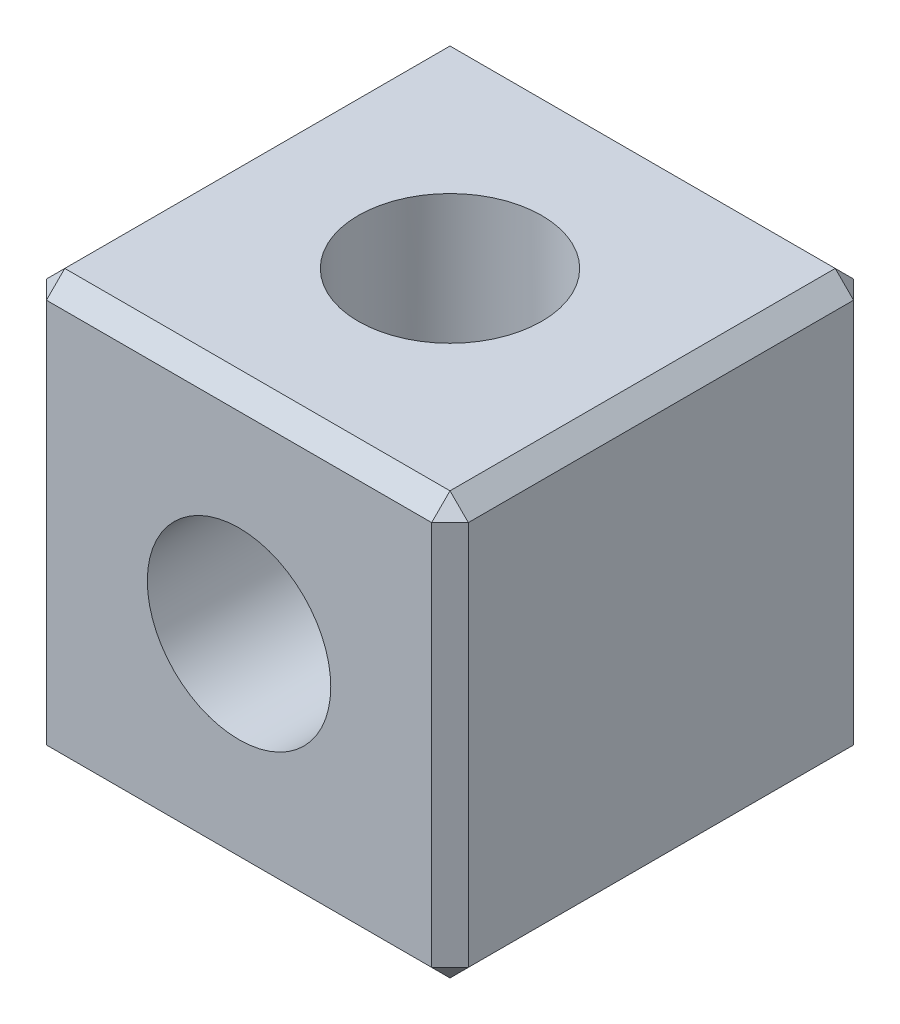
SolidWorks part; units mm, degrees
ref_plane "Front Plane" through (0, 0, 0) normal (0, 0, 1) x (1, 0, 0)
ref_plane "Top Plane" through (0, 0, 0) normal (0, 1, 0) x (1, 0, 0)
ref_plane "Right Plane" through (0, 0, 0) normal (1, 0, 0) x (0, 0, -1)
sketch "Sketch1" plane through (0, 0, 0) normal (0, 0, 1) x (1, 0, 0)
  line L1 (-11.5, -11.5) -> (11.5, -11.5)
  line L2 (-11.5, -11.5) -> (-11.5, 11.5)
  line L3 (-11.5, 11.5) -> (11.5, 11.5)
  line L4 (11.5, -11.5) -> (11.5, 11.5)
  line L5 (-11.5, -11.5) -> (11.5, 11.5) construction
  line L6 (-11.5, 11.5) -> (11.5, -11.5) construction
  point P0 (0, 0)
  dimension "D1" = 23
  dimension "D2" = 23
extrude "Boss-Extrude1" add sketch "Sketch1" along normal blind 23
sketch "Sketch2" plane through (0, 0, 23) normal (0, 0, 1) x (1, 0, 0)
  circle A0 centre (0, 0) radius 5
  dimension "D1" = 10
extrude "Cut-Extrude1" cut sketch "Sketch2" against normal blind 23
sketch "Sketch3" plane through (0, 11.5, 0) normal (0, 1, 0) x (1, 0, 0)
  line L0 (0, 0) -> (0, -23)
  line L1 (11.5, -23) -> (-11.5, -23) construction
  circle A0 centre (0, -11.5) radius 5
  dimension "D1" = 10
extrude "Cut-Extrude2" cut sketch "Sketch3" against normal blind 23 contours L0 A0 | L0 A0
chamfer "Chamfer1" distance 1 angle 45 12 edges at (-11.5, 11.5, 11.5) (-11.5, 0, 0) (11.5, 0, 23) (11.5, 0, 0) (0, -11.5, 0) (11.5, -11.5, 11.5) (-11.5, -11.5, 11.5) (0, -11.5, 23) (-11.5, 0, 23) (0, 11.5, 23) (11.5, 11.5, 11.5) (0, 11.5, 0)
